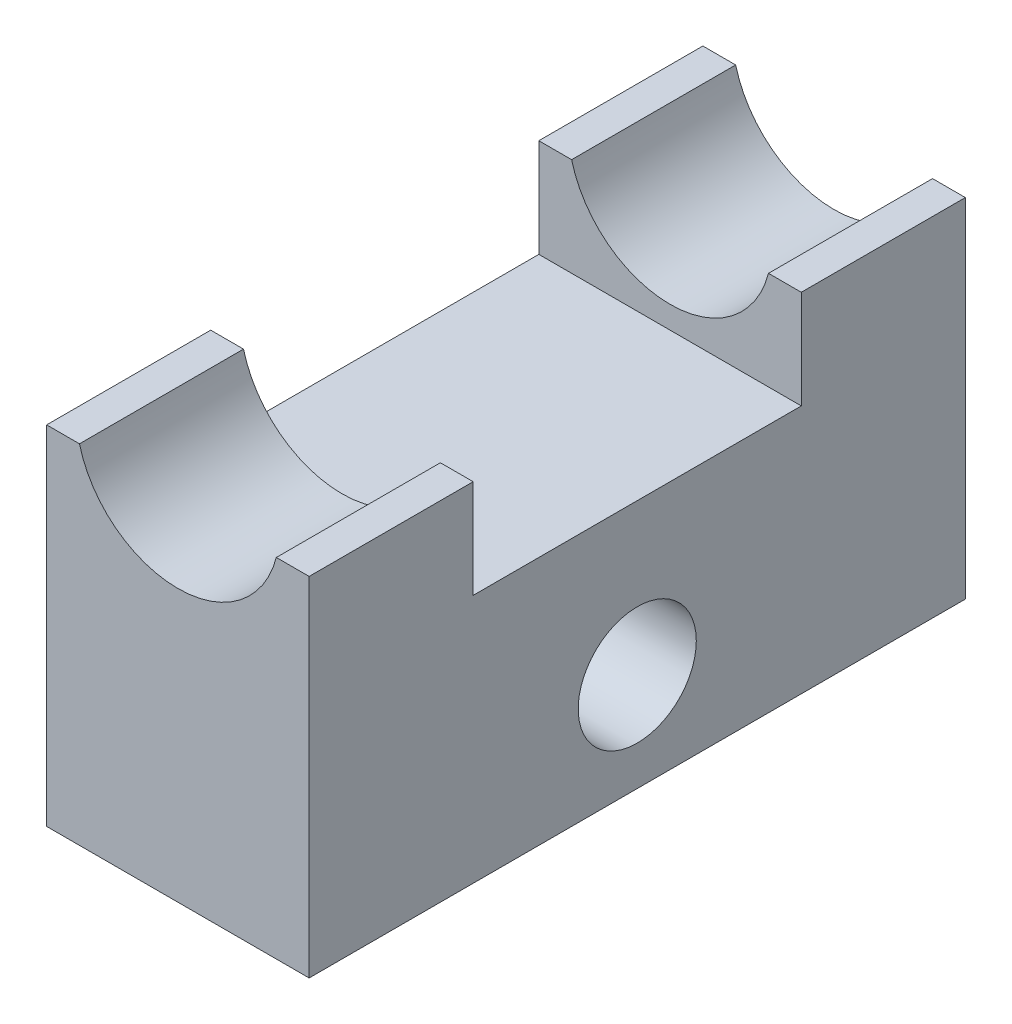
SolidWorks part; units mm, degrees
material "2024-O"
ref_plane "Plan de face" through (0, 0, 0) normal (0, 0, 1) x (1, 0, 0)
ref_plane "Plan de dessus" through (0, 0, 0) normal (0, 1, 0) x (1, 0, 0)
ref_plane "Plan de droite" through (0, 0, 0) normal (1, 0, 0) x (0, 0, -1)
sketch "Esquisse1" plane through (0, 0, 0) normal (0, 0, 1) x (1, 0, 0)
  line L1 (1005.3924, 375.6191) -> (1000.3924, 375.6191)
  line L2 (1000.3924, 375.6191) -> (1000.3924, 322.6191)
  line L3 (1000.3924, 322.6191) -> (1040.3924, 322.6191)
  line L4 (1040.3924, 322.6191) -> (1040.3924, 375.6191)
  line L5 (1040.3924, 375.6191) -> (1035.3924, 375.6191)
  arc A0 (1005.3924, 375.6191) -> (1035.3924, 375.6191) centre (1020.3924, 379.5242) ccw
  dimension "D2" = 5
  dimension "D1" = 15.5
  dimension "D3" = 5
  dimension "D4" = 53
  dimension "D5" = 40
extrude "Boss.-Extru.1" add sketch "Esquisse1" along normal blind 100
sketch "Esquisse2" plane through (1040.3924, 0, 0) normal (1, 0, 0) x (0, 0, -1)
  line L0 (-100, 322.6191) -> (0, 322.6191) construction
  line L1 (-100, 375.6191) -> (0, 375.6191) construction
  line L2 (-75, 375.6191) -> (-25, 375.6191)
  line L3 (-75, 375.6191) -> (-75, 360.6191)
  line L4 (-75, 360.6191) -> (-25, 360.6191)
  line L5 (-25, 375.6191) -> (-25, 360.6191)
  line L6 (-100, 322.6191) -> (-100, 375.6191) construction
  line L7 (0, 322.6191) -> (0, 375.6191) construction
  line L8 (-100, 375.6191) -> (-100, 322.6191) construction
  circle A0 centre (-50, 337.6191) radius 9
  dimension "D1" = 18
  dimension "D2" = 15
  dimension "D3" = 25
  dimension "D4" = 25
  dimension "D5" = 15
  dimension "D6" = 50
extrude "Enlèv. mat.-Extru.1" cut sketch "Esquisse2" against normal blind 100
